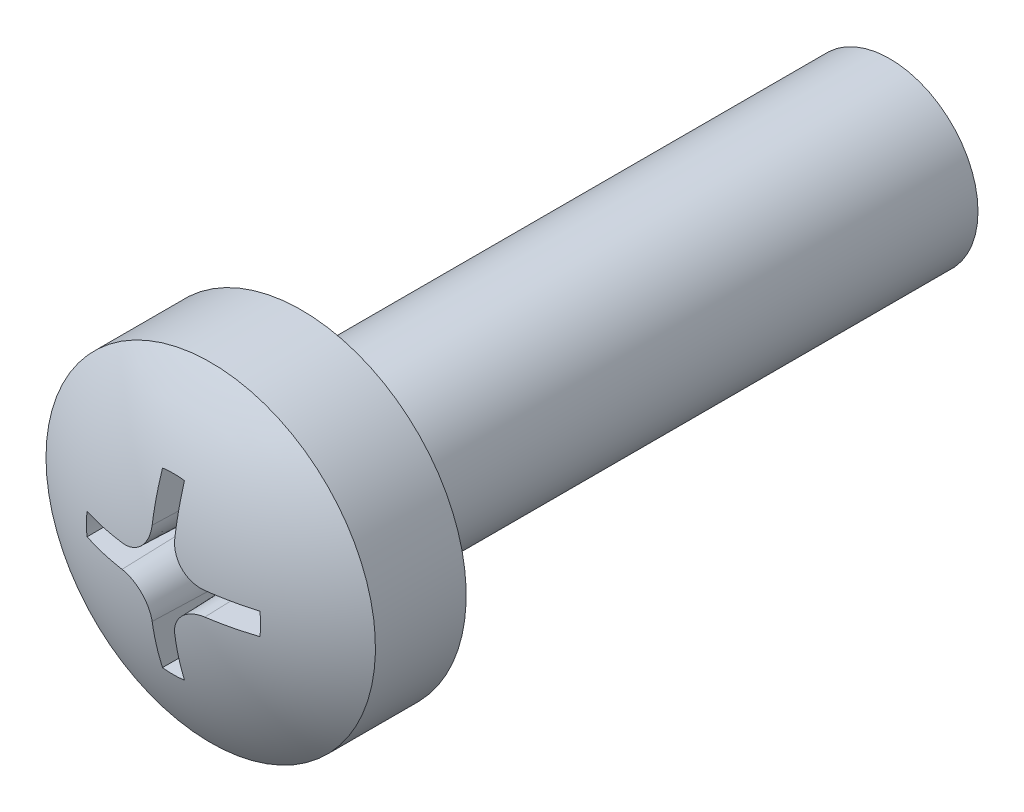
SolidWorks part; units mm, degrees
material "普通碳钢"
ref_plane "Plane1" through (0, 0, 0) normal (0, 0, 1) x (1, 0, 0)
ref_plane "Plane2" through (0, 0, 0) normal (0, 1, 0) x (1, 0, 0)
ref_plane "Plane3" through (0, 0, 0) normal (1, 0, 0) x (0, 0, -1)
sketch "Sketch1" plane through (0, 0, 0) normal (0, 0, 1) x (1, 0, 0)
  circle A0 centre (0, 0) radius 1.5
  dimension "D1" = 3
extrude "Base-Extrude" add sketch "Sketch1" along normal blind 10
sketch "Sketch6" plane through (0, 0, 0) normal (0, 1, 0) x (1, 0, 0)
  line L0 (0, 0.3936) -> (0, -34.4908) construction
  line L1 (0, -10) -> (0, 0) construction
  line L2 (0, -10) -> (2.8, -10)
  line L3 (2.8, -10) -> (2.8, -11.5425)
  line L4 (0, -12.4) -> (0, -10)
  line L5 (-1.5, -10) -> (1.5, -10) construction
  arc A0 (2.8, -11.5425) -> (0, -12.4) centre (0, -7.4) cw
  dimension "D1" = 2.4
  dimension "D9" = 5
  dimension "D8" = 2.8
revolve "Boss-Revolve2" add sketch "Sketch6" angle 360 about L0
ref_plane "Plane6" through (0, 0, 12.7) normal (0, 0, -1) x (-1, 0, 0)
sketch "Sketch7" plane through (0, 0, 12.7) normal (0, 0, -1) x (-1, 0, 0)
  line L0 (-7.1, 0) -> (5.9, 0) construction
  line L1 (0, 7.5) -> (0, -7) construction
  line L2 (0.205, 1.4859) -> (0.205, 0.7082)
  line L3 (0, 0) -> (4.9858, 4.9858) construction
  line L4 (1.4859, 0.205) -> (0.703, 0.2082)
  line L5 (1.4859, -0.205) -> (0.703, -0.2082)
  line L6 (0.205, -1.4859) -> (0.205, -0.7082)
  line L7 (-0.205, -1.4859) -> (-0.205, -0.7082)
  line L8 (-1.4859, -0.205) -> (-0.703, -0.2082)
  line L9 (-1.4859, 0.205) -> (-0.703, 0.2082)
  line L10 (-0.205, 1.4859) -> (-0.205, 0.7082)
  arc A0 (-0.205, 1.4859) -> (0.205, 1.4859) centre (0, 0) cw
  arc A1 (1.4859, -0.205) -> (1.4859, 0.205) centre (0, 0) ccw
  arc A2 (0.205, 0.7082) -> (0.703, 0.2082) centre (0.705, 0.7082) ccw
  arc A3 (-0.205, 0.7082) -> (-0.703, 0.2082) centre (-0.705, 0.7082) cw
  arc A4 (-0.205, -1.4859) -> (0.205, -1.4859) centre (0, 0) ccw
  arc A5 (-0.205, -0.7082) -> (-0.703, -0.2082) centre (-0.705, -0.7082) ccw
  arc A6 (-1.4859, -0.205) -> (-1.4859, 0.205) centre (0, 0) cw
  arc A7 (0.703, -0.2082) -> (0.205, -0.7082) centre (0.705, -0.7082) ccw
  dimension "D1" = 0.5
  dimension "D10" = 1.5
  dimension "D11" = 0.41
extrude "Cut-Extrude1" cut sketch "Sketch7" along normal blind 1.8 draft 2
